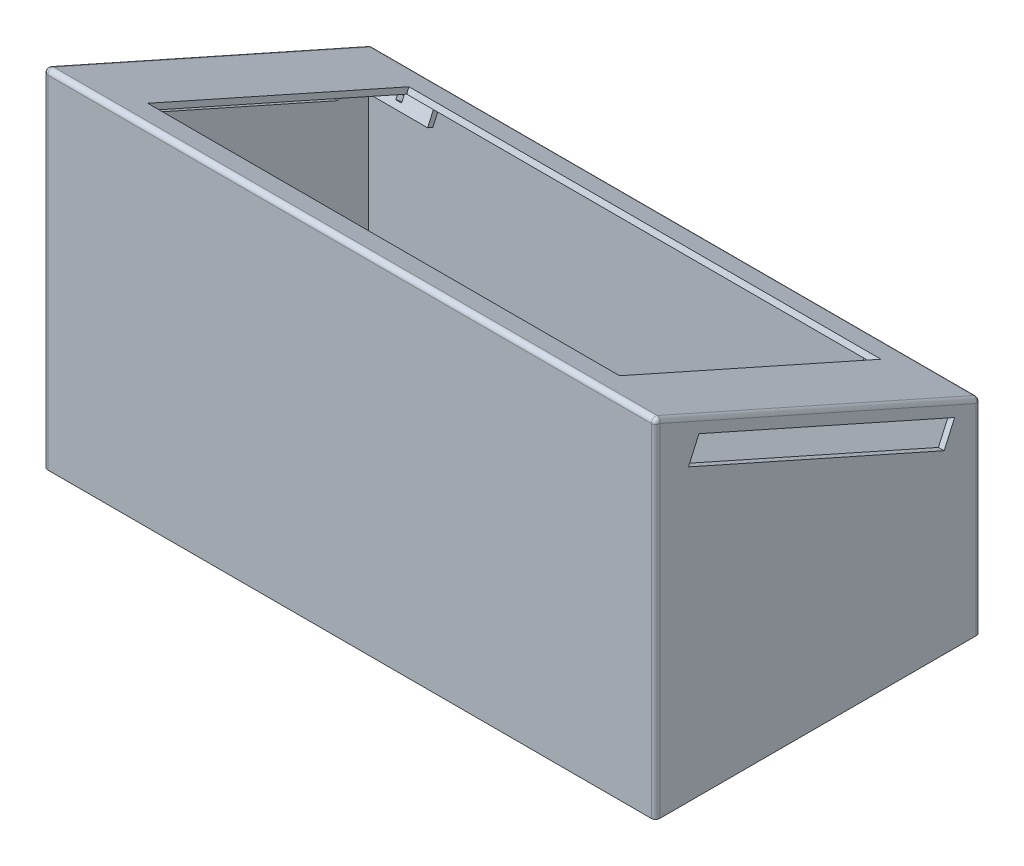
SolidWorks part; units mm, degrees
ref_plane "前视基准面" through (0, 0, 0) normal (0, 0, 1) x (1, 0, 0)
ref_plane "上视基准面" through (0, 0, 0) normal (0, 1, 0) x (1, 0, 0)
ref_plane "右视基准面" through (0, 0, 0) normal (1, 0, 0) x (0, 0, -1)
other "Configuration Table"
sketch "草图2" plane through (0, 0, 0) normal (1, 0, 0) x (0, 0, -1)
  line L0 (0, 0) -> (0, 118.8084)
  line L1 (0, 118.8084) -> (109.6255, 70)
  line L2 (109.6255, 70) -> (109.6255, 0)
  line L3 (109.6255, 0) -> (0, 0)
  line L4 (109.6255, 70) -> (0, 70) construction
  dimension "D1" = 24
  dimension "D2" = 70
  dimension "D3" = 120
extrude "凸台-拉伸1" add sketch "草图2" along normal blind 210
sketch "草图3" plane through (0, 99.1534, -44.1459) normal (0, 0.9135, -0.4067) x (1, 0, 0)
  line L0 (210, 71.6763) -> (0, -48.3237) construction
  line L2 (22.5, 61.6763) -> (187.5, 61.6763)
  line L3 (22.5, 61.6763) -> (22.5, -38.3237)
  line L4 (0, 71.6763) -> (0, -48.3237)
  line L5 (0, -48.3237) -> (210, -48.3237)
  line L6 (210, -48.3237) -> (210, 71.6763)
  line L7 (210, 71.6763) -> (0, 71.6763)
  line L8 (0, 71.6763) -> (0, -48.3237) construction
  line L9 (0, -48.3237) -> (210, -48.3237) construction
  line L10 (210, -48.3237) -> (210, 71.6763) construction
  line L11 (210, 71.6763) -> (0, 71.6763) construction
  line L12 (22.5, -38.3237) -> (187.5, -38.3237)
  line L13 (187.5, 61.6763) -> (187.5, -38.3237)
  line L14 (22.5, 61.6763) -> (187.5, -38.3237) construction
  line L15 (22.5, -38.3237) -> (187.5, 61.6763) construction
  point P2 (105, 11.6763)
  dimension "D2" = 120
  dimension "D3" = 210
  dimension "D4" = 165
  dimension "D5" = 100
  dimension "D1" = 0
shell "抽壳1" thickness 2
extrude "切除-拉伸2" cut sketch "草图3" along normal blind 2
sketch "草图5" plane through (0, 99.1534, -44.1459) normal (0, -0.9135, 0.4067) x (1, 0, 0)
  line L0 (187.5, -61.6763) -> (22.5, -61.6763) construction
  line L1 (187.5, 38.3237) -> (187.5, -61.6763) construction
  line L2 (22.5, -61.6763) -> (22.5, 38.3237) construction
  line L3 (22.5, 38.3237) -> (187.5, 38.3237) construction
  line L4 (187.5, -61.6763) -> (22.5, -61.6763) construction
  line L5 (187.5, 38.3237) -> (187.5, -61.6763) construction
  line L6 (22.5, -61.6763) -> (22.5, 38.3237) construction
  line L7 (22.5, 38.3237) -> (187.5, 38.3237) construction
  line L8 (187.5, 38.3237) -> (22.5, -61.6763) construction
  line L10 (9.75, 41.0737) -> (200.25, 41.0737) construction
  line L11 (9.75, 41.0737) -> (9.75, -64.4263) construction
  line L12 (9.75, -64.4263) -> (200.25, -64.4263) construction
  line L13 (200.25, 41.0737) -> (200.25, -64.4263) construction
  line L14 (9.75, 41.0737) -> (200.25, -64.4263) construction
  line L15 (9.75, -64.4263) -> (200.25, 41.0737) construction
  line L16 (9.75, 43.0737) -> (29.75, 43.0737)
  line L17 (29.75, 43.0737) -> (29.75, 41.0737)
  line L18 (29.75, 41.0737) -> (9.75, 41.0737)
  line L25 (105, -11.6763) -> (105, 70.6346) construction
  line L26 (105, 41.0737) -> (95, 41.0737) construction
  line L27 (95, 41.0737) -> (95, 43.0737) construction
  line L28 (95, 43.0737) -> (115, 43.0737) construction
  line L29 (115, 43.0737) -> (115, 41.0737) construction
  line L30 (115, 41.0737) -> (105, 41.0737) construction
  line L31 (180.25, 43.0737) -> (180.25, 41.0737)
  line L32 (180.25, 41.0737) -> (200.25, 41.0737)
  line L34 (200.25, 43.0737) -> (180.25, 43.0737)
  line L35 (105, -11.6763) -> (58.9335, -11.6763) construction
  line L36 (180.25, -66.4263) -> (180.25, -64.4263)
  line L38 (180.25, -64.4263) -> (200.25, -64.4263)
  line L39 (200.25, -66.4263) -> (180.25, -66.4263)
  line L40 (115, -64.4263) -> (105, -64.4263) construction
  line L41 (115, -66.4263) -> (115, -64.4263) construction
  line L42 (105, -64.4263) -> (95, -64.4263) construction
  line L43 (95, -66.4263) -> (115, -66.4263) construction
  line L44 (95, -64.4263) -> (95, -66.4263) construction
  line L45 (29.75, -66.4263) -> (29.75, -64.4263)
  line L46 (29.75, -64.4263) -> (9.75, -64.4263)
  line L47 (9.75, -66.4263) -> (29.75, -66.4263)
  line L49 (200.25, 43.0737) -> (202.25, 43.0737)
  line L50 (202.25, 43.0737) -> (202.25, 21.0737)
  line L51 (202.25, 21.0737) -> (200.25, 21.0737)
  line L52 (200.25, 21.0737) -> (200.25, 41.0737)
  line L53 (7.75, 21.0737) -> (9.75, 21.0737)
  line L54 (9.75, 21.0737) -> (9.75, 41.0737)
  line L55 (7.75, 43.0737) -> (7.75, 21.0737)
  line L56 (9.75, 43.0737) -> (7.75, 43.0737)
  line L57 (7.75, -44.4263) -> (9.75, -44.4263)
  line L58 (7.75, -66.4263) -> (7.75, -44.4263)
  line L59 (9.75, -66.4263) -> (7.75, -66.4263)
  line L60 (9.75, -44.4263) -> (9.75, -64.4263)
  line L61 (202.25, -44.4263) -> (200.25, -44.4263)
  line L62 (200.25, -66.4263) -> (202.25, -66.4263)
  line L63 (200.25, -44.4263) -> (200.25, -64.4263)
  line L64 (202.25, -66.4263) -> (202.25, -44.4263)
  point P3 (105, -11.6763)
  dimension "D1" = 105.5
  dimension "D2" = 190.5
  dimension "D3" = 2
  dimension "D4" = 2
  dimension "D5" = 20
  dimension "D6" = 10
  dimension "D7" = 10
  dimension "D8" = 2
  dimension "D9" = 22
extrude "凸台-拉伸2" add sketch "草图5" along normal blind 6
sketch "草图6" plane through (0, 16.7062, 37.5227) normal (0, -0.4067, -0.9135) x (-1, 0, 0)
  line L0 (-9.75, 108.5369) -> (-29.75, 102.5369) construction
  line L1 (-22.4665, 106.7369) -> (-20.4665, 106.7369)
  line L4 (-9.75, 108.5369) -> (-29.75, 108.5369)
  line L5 (-29.75, 108.5369) -> (-29.75, 102.5369)
  line L6 (-29.75, 102.5369) -> (-9.75, 102.5369)
  line L7 (-9.75, 102.5369) -> (-9.75, 108.5369)
  line L8 (-9.75, 108.5369) -> (-29.75, 108.5369) construction
  line L9 (-29.75, 108.5369) -> (-29.75, 102.5369) construction
  line L10 (-29.75, 102.5369) -> (-9.75, 102.5369) construction
  line L11 (-9.75, 102.5369) -> (-9.75, 108.5369) construction
  dimension "D2" = 1.8
  dimension "D3" = 2
  dimension "D1" = 0
sketch "草图7" plane through (0, 93.6721, -41.7055) normal (0, -0.9135, 0.4067) x (1, 0, 0)
  line L0 (9.75, 43.9246) -> (19.75, 43.9246) construction
  line L1 (9.75, 41.0737) -> (2.9722, 41.0737) construction
  line L2 (5.1882, 41.0737) -> (5.1882, 31.0737) construction
  line L3 (19.75, 43.0737) -> (7.75, 31.0737) construction
  line L5 (9.75, 31.0737) -> (19.75, 41.0737) construction
  line L6 (9.75, 21.0737) -> (9.75, 41.0737)
  line L7 (9.75, 41.0737) -> (29.75, 41.0737)
  line L8 (29.75, 41.0737) -> (29.75, 43.0737)
  line L9 (29.75, 43.0737) -> (7.75, 43.0737)
  line L10 (7.75, 43.0737) -> (7.75, 21.0737)
  line L11 (7.75, 21.0737) -> (9.75, 21.0737)
  line L12 (9.75, 21.0737) -> (9.75, 41.0737) construction
  line L13 (9.75, 41.0737) -> (29.75, 41.0737) construction
  line L14 (29.75, 41.0737) -> (29.75, 43.0737) construction
  line L15 (29.75, 43.0737) -> (7.75, 43.0737) construction
  line L16 (7.75, 43.0737) -> (7.75, 21.0737) construction
  line L17 (7.75, 21.0737) -> (9.75, 21.0737) construction
  line L19 (19.75, 41.0737) -> (21.75, 43.0737) construction
  line L20 (21.75, 43.0737) -> (19.75, 43.0737) construction
  line L21 (9.75, 31.0737) -> (7.75, 29.0737) construction
  line L22 (7.75, 29.0737) -> (7.75, 31.0737) construction
  dimension "D2" = 10
  dimension "D3" = 10
  dimension "D4" = 2
  dimension "D1" = 0
ref_plane "基准面1" through (0, 97.509, -43.4138) normal (0, -0.9135, 0.4067) x (-1, 0, 0)
sketch "草图8" plane through (0, 97.509, -43.4138) normal (0, -0.9135, 0.4067) x (-1, 0, 0)
  line L0 (-19.75, -41.0737) -> (-21.75, -43.0737) construction
  line L1 (-19.75, -43.0737) -> (-7.75, -31.0737) construction
  line L3 (-9.75, -31.0737) -> (-7.75, -29.0737) construction
  line L4 (-9.75, -31.0737) -> (-19.75, -41.0737) construction
  line L5 (-19.75, -41.0737) -> (-21.75, -43.0737)
  line L6 (-19.75, -43.0737) -> (-7.75, -31.0737)
  line L7 (-7.75, -29.0737) -> (-7.75, -31.0737)
  line L8 (-9.75, -31.0737) -> (-7.75, -29.0737)
  line L9 (-9.75, -31.0737) -> (-19.75, -41.0737)
  line L10 (-21.75, -43.0737) -> (-19.75, -43.0737)
  line L11 (-187.5, 61.6763) -> (-22.5, 61.6763) construction
  line L12 (-187.5, -38.3237) -> (-187.5, 61.6763) construction
  line L13 (-187.5, 61.6763) -> (-22.5, 61.6763) construction
  line L14 (-187.5, -38.3237) -> (-187.5, 61.6763) construction
  line L15 (-105, 61.6763) -> (-105, -29.0737) construction
  line L16 (-187.5, 11.6763) -> (-73.2823, 11.6763) construction
  line L17 (-19.75, 64.4263) -> (-21.75, 66.4263)
  line L18 (-21.75, 66.4263) -> (-19.75, 66.4263)
  line L19 (-19.75, 66.4263) -> (-7.75, 54.4263)
  line L20 (-7.75, 52.4263) -> (-7.75, 54.4263)
  line L21 (-9.75, 54.4263) -> (-7.75, 52.4263)
  line L22 (-9.75, 54.4263) -> (-19.75, 64.4263)
  line L23 (-190.25, -41.0737) -> (-188.25, -43.0737)
  line L24 (-188.25, -43.0737) -> (-190.25, -43.0737)
  line L25 (-190.25, -43.0737) -> (-202.25, -31.0737)
  line L26 (-200.25, -31.0737) -> (-190.25, -41.0737)
  line L27 (-200.25, -31.0737) -> (-202.25, -29.0737)
  line L28 (-202.25, -29.0737) -> (-202.25, -31.0737)
  line L29 (-200.25, 54.4263) -> (-202.25, 52.4263)
  line L30 (-202.25, 52.4263) -> (-202.25, 54.4263)
  line L31 (-200.25, 54.4263) -> (-190.25, 64.4263)
  line L32 (-190.25, 66.4263) -> (-202.25, 54.4263)
  line L33 (-190.25, 64.4263) -> (-188.25, 66.4263)
  line L34 (-188.25, 66.4263) -> (-190.25, 66.4263)
extrude "切除-拉伸3" cut sketch "草图8" along normal blind 2
sketch "草图10" plane through (-2, 0, 0) normal (-1, 0, 0) x (0, 0, 1)
  line L0 (-98.9021, 61.6387) -> (-9.5218, 101.4334)
  line L1 (-98.9021, 61.6387) -> (-102.5628, 69.8606)
  line L2 (-102.5628, 69.8606) -> (-13.1824, 109.6553)
  line L3 (-13.1824, 109.6553) -> (-9.5218, 101.4334)
  line L4 (-111.6255, 0) -> (2, 0)
  line L5 (2, 0) -> (2, 121.8881)
  line L6 (2, 121.8881) -> (-111.6255, 71.2988)
  line L7 (-111.6255, 71.2988) -> (-111.6255, 0)
  line L8 (-111.6255, 0) -> (2, 0) construction
  line L9 (2, 0) -> (2, 121.8881) construction
  line L10 (2, 121.8881) -> (-111.6255, 71.2988) construction
  line L11 (-111.6255, 71.2988) -> (-111.6255, 0) construction
  dimension "D2" = 14
  dimension "D3" = 5
  dimension "D1" = 0
extrude "切除-拉伸4" cut sketch "草图10" against normal blind 2
sketch "草图11" plane through (212, 0, 0) normal (1, 0, 0) x (0, 0, -1)
  line L0 (9.5218, 101.4334) -> (13.1824, 109.6553) construction
  line L1 (102.5628, 69.8606) -> (98.9021, 61.6387) construction
  line L2 (13.1824, 109.6553) -> (102.5628, 69.8606) construction
  line L3 (98.9021, 61.6387) -> (9.5218, 101.4334) construction
  line L4 (9.5218, 101.4334) -> (13.1824, 109.6553)
  line L5 (102.5628, 69.8606) -> (98.9021, 61.6387)
  line L6 (13.1824, 109.6553) -> (102.5628, 69.8606)
  line L7 (98.9021, 61.6387) -> (9.5218, 101.4334)
extrude "切除-拉伸5" cut sketch "草图11" against normal blind 2
fillet "圆角1" radius 1.5 8 edges at (-2, 60.9441, 2) (212, 60.9441, 2) (212, 35.6494, -111.6255) (-2, 35.6494, -111.6255) (105, 71.2988, -111.6255) (212, 96.5935, -54.8127) (105, 121.8881, 2) (-2, 96.5935, -54.8127)
